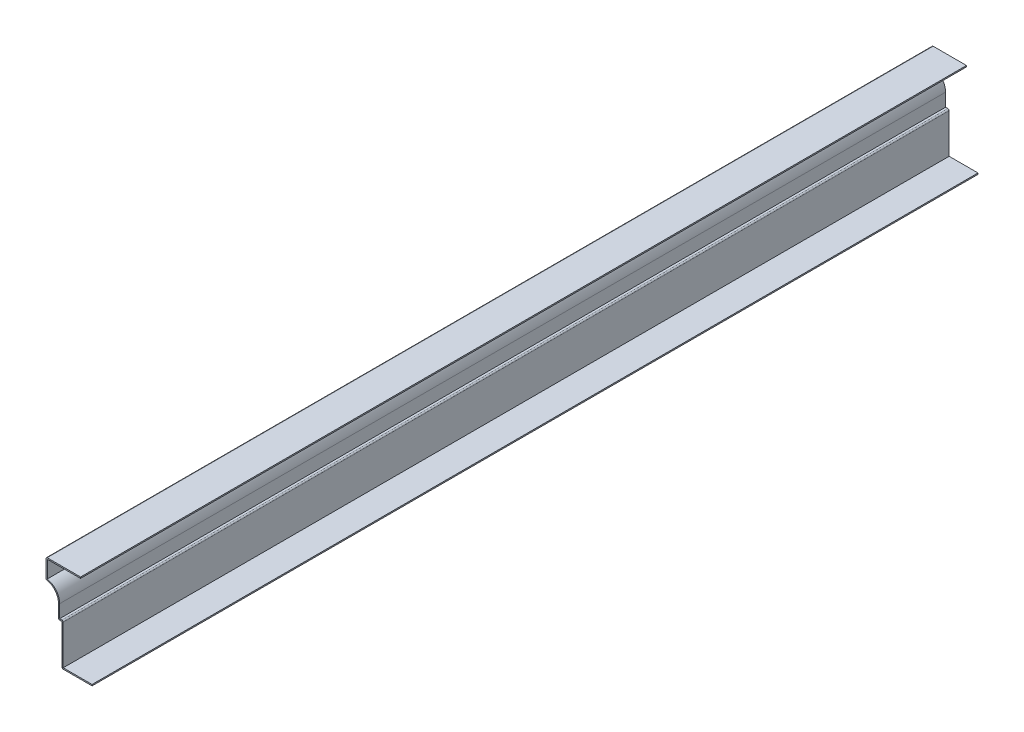
SolidWorks part; units mm, degrees
ref_plane "Front Plane" through (0, 0, 0) normal (0, 0, 1) x (1, 0, 0)
ref_plane "Top Plane" through (0, 0, 0) normal (0, 1, 0) x (1, 0, 0)
ref_plane "Right Plane" through (0, 0, 0) normal (1, 0, 0) x (0, 0, -1)
sketch "Sketch1" plane through (0, 0, 0) normal (0, 0, 1) x (1, 0, 0)
  line L0 (0, 0) -> (-26.9875, 0)
  line L1 (-26.9875, 0) -> (-26.9875, 36.5125)
  line L2 (-26.9875, 36.5125) -> (-30.1625, 36.5125)
  line L3 (-30.1625, 36.5125) -> (-30.1625, 49.3121)
  line L4 (-41.275, 61.9125) -> (-41.275, 79.375)
  line L5 (-41.275, 79.375) -> (-10.3188, 79.375)
  arc A0 (-30.1625, 49.3121) -> (-41.275, 61.9125) centre (-42.8625, 49.3121) ccw
  dimension "D9" = 12.7
  dimension "D1" = 79.375
  dimension "D2" = 41.275
  dimension "D3" = 30.9562
  dimension "D4" = 17.4625
  dimension "D5" = 26.9875
  dimension "D6" = 36.5125
  dimension "D7" = 3.175
  dimension "D8" = 25.4
extrude "Extrude-Thin1" add sketch "Sketch1" against normal blind 793.75 thin
fillet "Fillet1" radius 1.143 5 edges at (-26.9875, 0, -396.875) (-25.8445, 37.6555, -396.875) (-30.1625, 36.5125, -396.875) (-41.275, 61.9125, -396.875) (-41.275, 79.375, -396.875)
